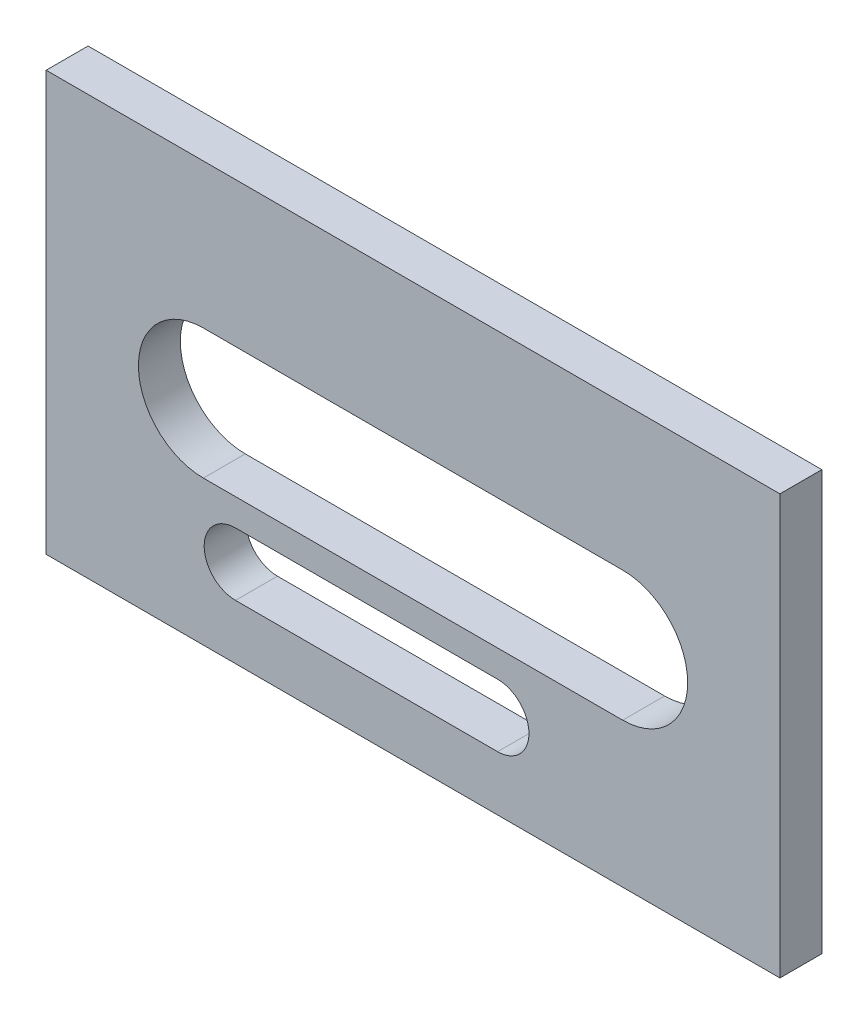
SolidWorks part; units mm, degrees
ref_plane "Plan de face" through (0, 0, 0) normal (0, 0, 1) x (1, 0, 0)
ref_plane "Plan de dessus" through (0, 0, 0) normal (0, 1, 0) x (1, 0, 0)
ref_plane "Plan de droite" through (0, 0, 0) normal (1, 0, 0) x (0, 0, -1)
sketch "Esquisse8" plane through (0, 0, 0) normal (0, 0, 1) x (1, 0, 0)
  line L0 (-193.6012, 56.4894) -> (-113.6012, 56.4894) construction
  line L1 (-223.6012, 96.4894) -> (-83.6012, 96.4894)
  line L2 (-223.6012, 96.4894) -> (-223.6012, 16.4894)
  line L3 (-223.6012, 16.4894) -> (-83.6012, 16.4894)
  line L4 (-83.6012, 96.4894) -> (-83.6012, 16.4894)
  line L5 (-223.6012, 96.4894) -> (-83.6012, 16.4894) construction
  line L6 (-223.6012, 16.4894) -> (-83.6012, 96.4894) construction
  line L7 (-193.6012, 68.8874) -> (-113.6012, 68.8874)
  line L8 (-193.6012, 44.0914) -> (-113.6012, 44.0914)
  line L9 (-187.47, 32.938) -> (-137.47, 32.938) construction
  line L10 (-187.47, 38.9227) -> (-137.47, 38.9227)
  line L11 (-187.47, 26.9532) -> (-137.47, 26.9532)
  arc A0 (-193.6012, 68.8874) -> (-193.6012, 44.0914) centre (-193.6012, 56.4894) ccw
  arc A1 (-113.6012, 44.0914) -> (-113.6012, 68.8874) centre (-113.6012, 56.4894) ccw
  arc A2 (-187.47, 38.9227) -> (-187.47, 26.9532) centre (-187.47, 32.938) ccw
  arc A3 (-137.47, 26.9532) -> (-137.47, 38.9227) centre (-137.47, 32.938) ccw
  point P0 (-153.6012, 56.4894)
  point P7 (-153.6012, 56.4894)
  point P14 (-162.47, 32.938)
extrude "Boss.-Extru.7" add sketch "Esquisse8" along normal blind 8
